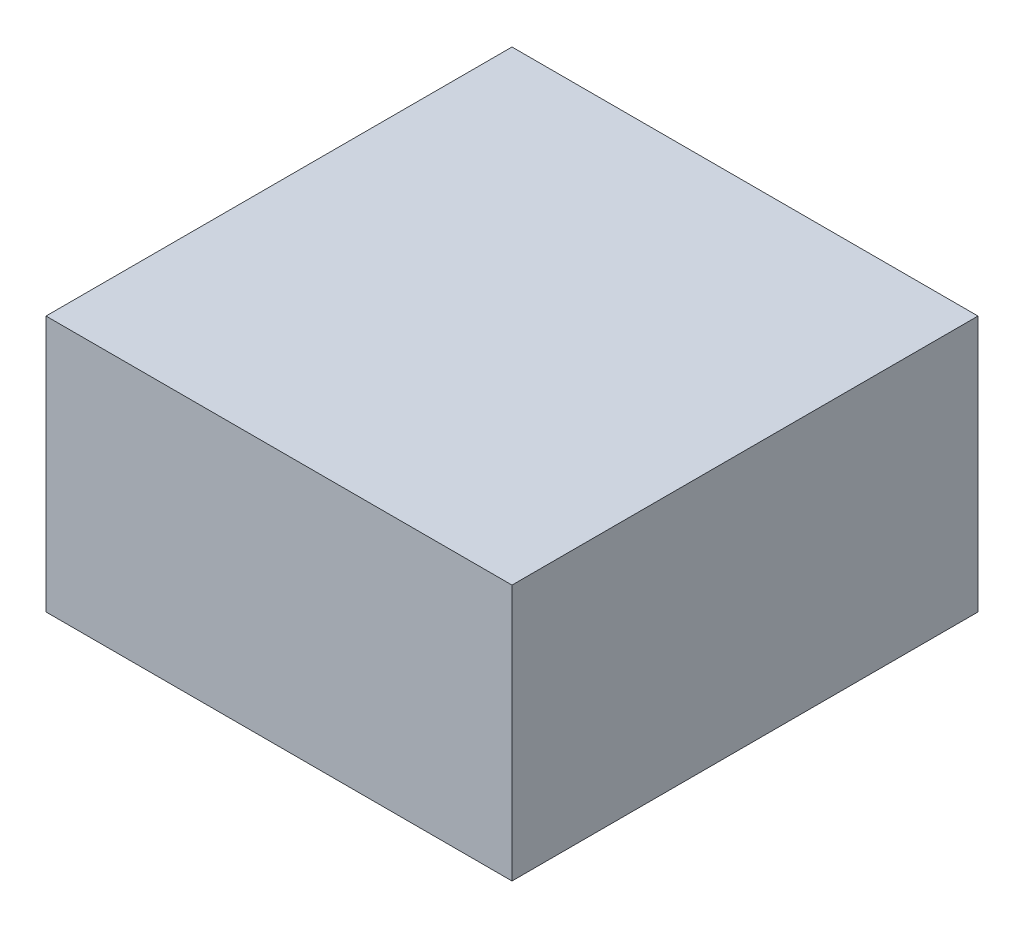
SolidWorks part; units mm, degrees
material "C (Grafito)"
ref_plane "Front" through (0, 0, 0) normal (0, 0, 1) x (1, 0, 0)
ref_plane "Top" through (0, 0, 0) normal (0, 1, 0) x (1, 0, 0)
ref_plane "Right" through (0, 0, 0) normal (1, 0, 0) x (0, 0, -1)
sketch "Croquis1" plane through (0, 0, 0) normal (0, 1, 0) x (1, 0, 0)
  line L1 (-0.5, 0.5) -> (0.5, 0.5)
  line L2 (-0.5, 0.5) -> (-0.5, -0.5)
  line L3 (-0.5, -0.5) -> (0.5, -0.5)
  line L4 (0.5, 0.5) -> (0.5, -0.5)
  line L5 (-0.5, 0.5) -> (0.5, -0.5) construction
  line L6 (-0.5, -0.5) -> (0.5, 0.5) construction
  point P0 (0, 0)
extrude "Saliente-Extruir1" add sketch "Croquis1" along normal blind 0.55
